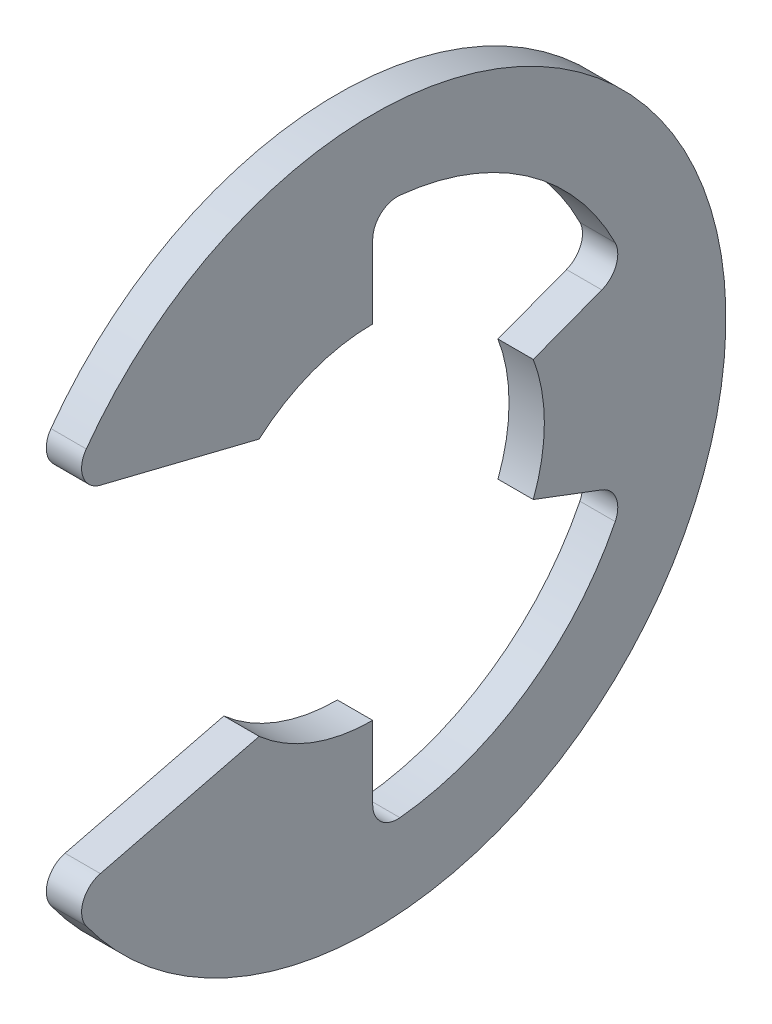
SolidWorks part; units mm, degrees
material "AISI 1020"
ref_plane "Front" through (0, 0, 0) normal (0, 0, 1) x (1, 0, 0)
ref_plane "Top" through (0, 0, 0) normal (0, 1, 0) x (1, 0, 0)
ref_plane "Right" through (0, 0, 0) normal (1, 0, 0) x (0, 0, -1)
sketch "Sketch1" plane through (0, 0, 0) normal (1, 0, 0) x (0, 0, -1)
  line L0 (-5.5002, -3.1733) -> (-2.0413, -2.3146)
  line L1 (-5.5002, 3.1733) -> (-2.0413, 2.3146)
  line L2 (0, -3.0861) -> (0, -4.8702)
  line L3 (0, 3.0861) -> (0, 4.8702)
  line L4 (2.8868, -1.0911) -> (4.5557, -1.7219)
  line L5 (2.8868, 1.0911) -> (4.5557, 1.7219)
  line L6 (0, 0) -> (-6.604, 0) construction
  line L7 (2.8868, 1.0911) -> (2.8868, -1.0911) construction
  line L8 (0, -3.0861) -> (-2.0413, -2.3146) construction
  line L9 (0, 6.35) -> (0, -6.35) construction
  circle A1 centre (0, 0) radius 6.604 construction
  circle A2 centre (0, 0) radius 3.0861 construction
  arc A3 (-5.5002, -3.1733) -> (-5.5002, 3.1733) centre (0, 0) ccw
  arc A4 (-2.0413, -2.3146) -> (0, -3.0861) centre (0, 0) ccw
  arc A5 (-2.0413, 2.3146) -> (0, 3.0861) centre (0, 0) cw
  arc A6 (2.8868, 1.0911) -> (2.8868, -1.0911) centre (0, 0) cw
  arc A7 (0, -4.8702) -> (4.5557, -1.7219) centre (0, 0) ccw
  arc A8 (4.5557, 1.7219) -> (0, 4.8702) centre (0, 0) ccw
  dimension "D1" = 4.8702
  dimension "OD" = 12.7
  dimension "L" = 13.208
  dimension "D" = 6.1722
  dimension "D2" = 3.5091
  dimension "D3" = 4.6292
extrude "Extrude1" add sketch "Sketch1" along normal mid plane 0.635
fillet "Fillet1" radius 0.4445 6 edges at (0, -4.8702, 0) (0, 4.8702, 0) (0, -3.1733, 5.5002) (0, 3.1733, 5.5002) (0, -1.7219, -4.5557) (0, 1.7219, -4.5557)
sketch "Sketch3" plane through (0, 0, 0) normal (0, 1, 0) x (1, 0, 0)
  line L0 (0.3683, 3.9624) -> (0.3683, 3.175)
  line L1 (0.3683, 3.175) -> (-0.3683, 3.175)
  line L2 (-0.3683, 3.175) -> (-0.3683, 3.9624)
  line L3 (-0.3683, 3.9624) -> (-7.9185, 3.9624)
  line L4 (3.1306, 0) -> (3.1306, 3.5687)
  line L5 (-7.9185, 3.9624) -> (-7.9185, 0)
  line L6 (-7.9185, 0) -> (3.1306, 0)
  line L8 (3.1306, 0) -> (3.1306, 3.9624) construction
  line L9 (3.1306, 3.9624) -> (0.3683, 3.9624) construction
  line L10 (3.1306, 0) -> (17.2631, 0) construction
  line L11 (3.1306, 3.5687) -> (2.7368, 3.9624)
  line L12 (2.7368, 3.9624) -> (0.3683, 3.9624)
  point P2 (0, 3.175)
  point P5 (0.3683, 3.5687)
  dimension "D1" = 2.7622
  dimension "Ds" = 7.9248
  dimension "Dg" = 6.35
  dimension "W" = 0.7366
  dimension "D2" = 11.049
  dimension "D3" = 45
revolve "Revolve2" [suppressed] add sketch "Sketch3" angle 360 about L10
equation "\"D2@Sketch3\" = \"W@Sketch3\"*15"
equation "\"D1@Sketch3\" = \"D2@Sketch3\"/4"
equation "\"D1@Sketch1\" = (\"OD@Sketch1\"+\"D@Sketch1\")/3.875"
equation "\"D3@Sketch1\" = \"D@Sketch1\"*.75"
equation "\"D1@Fillet1\" = \"D1@Extrude1\"*.7"
